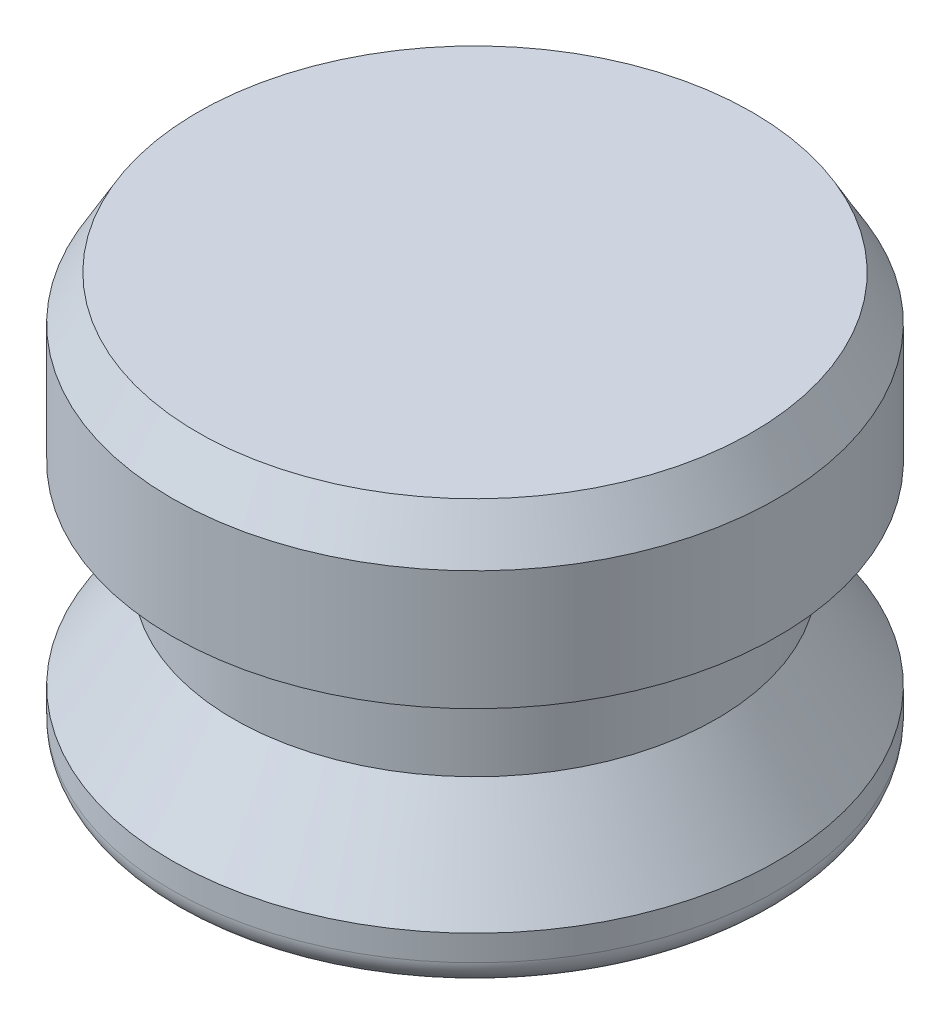
SolidWorks part; units mm, degrees
ref_plane "Front Plane" through (0, 0, 0) normal (0, 0, 1) x (1, 0, 0)
ref_plane "Top Plane" through (0, 0, 0) normal (0, 1, 0) x (1, 0, 0)
ref_plane "Right Plane" through (0, 0, 0) normal (1, 0, 0) x (0, 0, -1)
sketch "Sketch1" plane through (0, 0, 0) normal (0, 0, 1) x (1, 0, 0)
  line L0 (0, 0) -> (0, 12.7) construction
  line L1 (0, 0) -> (-9.398, 0)
  line L2 (-9.398, 0) -> (-9.398, 1.5875)
  line L4 (-7.493, 4.445) -> (-7.493, 7.62)
  line L5 (-7.493, 7.62) -> (-9.398, 7.62)
  line L6 (-9.398, 7.62) -> (-9.398, 12.7)
  line L7 (-9.398, 12.7) -> (0, 12.7)
  line L8 (-9.525, 16.6801) -> (-9.525, -9.6051) construction
  line L9 (0, 0) -> (0, 12.7)
  line L10 (-7.493, 4.445) -> (-9.398, 1.5875)
  dimension "D1" = 12.7
  dimension "D2" = 9.398
  dimension "D3" = 3.175
  dimension "D4" = 1.5875
  dimension "D5" = 9.525
  dimension "D6" = 7.493
  dimension "D7" = 7.62
revolve "Revolve1" add sketch "Sketch1" angle 360 about L9
fillet "Fillet1" radius 0.7937 1 edges at (0, 0, -9.398)
chamfer "Chamfer1" distance 0.7937 angle 60 1 edges at (0, 12.7, -9.398)
